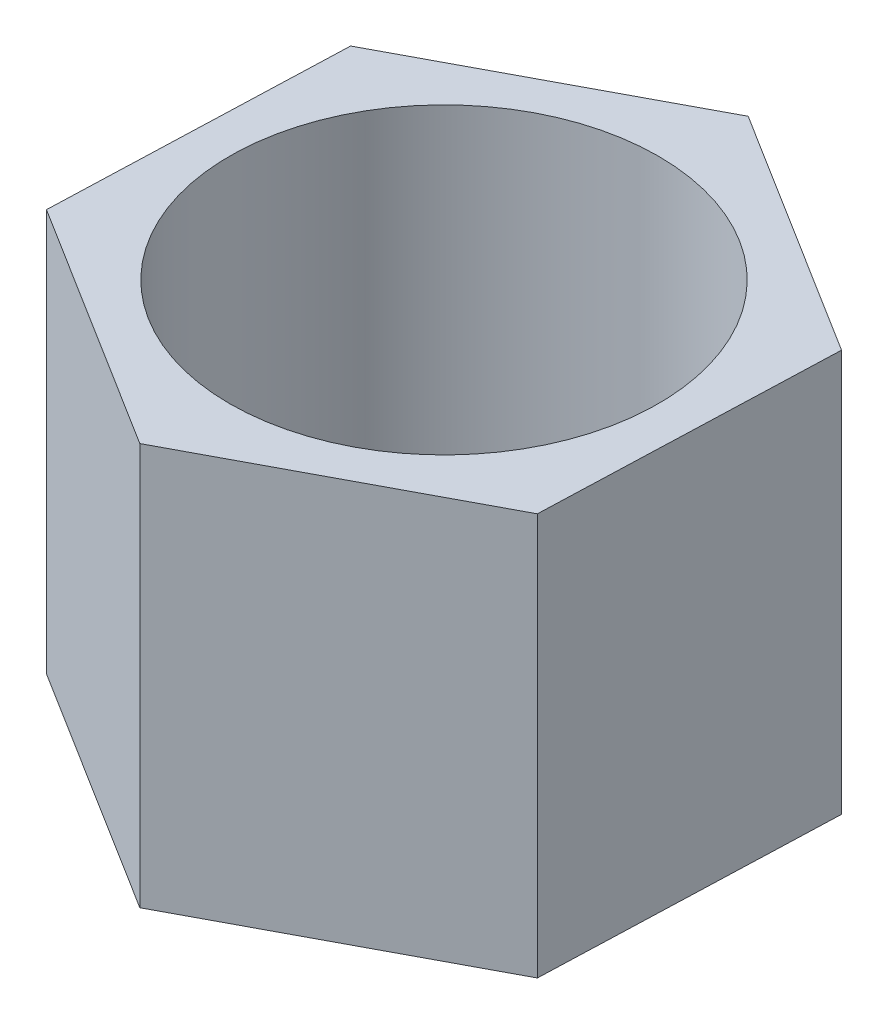
SolidWorks part; units mm, degrees
ref_plane "Спереди" through (0, 0, 0) normal (0, 0, 1) x (1, 0, 0)
ref_plane "Сверху" through (0, 0, 0) normal (0, 1, 0) x (1, 0, 0)
ref_plane "Справа" through (0, 0, 0) normal (1, 0, 0) x (0, 0, -1)
sketch "Sketch1" plane through (0, 0, 0) normal (0, 1, 0) x (1, 0, 0)
  line L1 (-9.3007, 5.8164) -> (-9.6875, -5.1464)
  line L2 (-9.6875, -5.1464) -> (-0.3869, -10.9628)
  line L3 (-0.3869, -10.9628) -> (9.3007, -5.8164)
  line L4 (9.3007, -5.8164) -> (9.6875, 5.1464)
  line L5 (9.6875, 5.1464) -> (0.3869, 10.9628)
  line L6 (0.3869, 10.9628) -> (-9.3007, 5.8164)
  circle A0 centre (0, 0) radius 8
  circle A1 centre (0, 0) radius 11 construction
  circle A2 centre (0, 0) radius 10.9697 construction
  dimension "D1" = 16
  dimension "D2" = 22
  dimension "D3" = 19
extrude "Boss-Extrude1" add sketch "Sketch1" along normal blind 15
